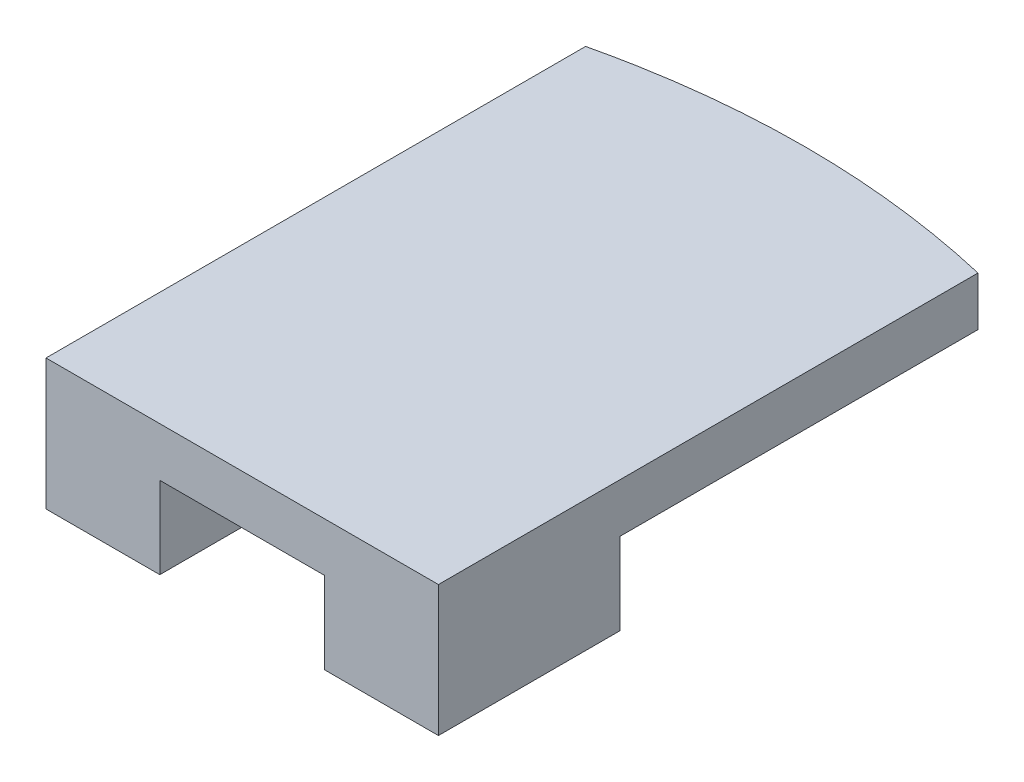
SolidWorks part; units mm, degrees
ref_plane "Front Plane" through (0, 0, 0) normal (0, 0, 1) x (1, 0, 0)
ref_plane "Top Plane" through (0, 0, 0) normal (0, 1, 0) x (1, 0, 0)
ref_plane "Right Plane" through (0, 0, 0) normal (1, 0, 0) x (0, 0, -1)
sketch "Sketch1" plane through (0, 0, 0) normal (0, 1, 0) x (1, 0, 0)
  line L0 (0, 0) -> (24, 0)
  line L1 (12, 0) -> (12, 35) construction
  line L2 (0, 0) -> (0, 33.6) construction
  line L3 (24, 0) -> (24, 33.6) construction
  line L4 (0, 0) -> (0, 33.6)
  line L5 (24, 0) -> (24, 33.6)
  spline S0 degree 2 poles (0, 33.6) (12, 36.4) (24, 33.6) knots 0 0 0 1 1 1
  dimension "D1" = 24
  dimension "D2" = 33.6
extrude "Boss-Extrude1" add sketch "Sketch1" along normal blind 3
sketch "Sketch4" plane through (0, 3, 0) normal (0, 1, 0) x (1, 0, 0)
  line L0 (24, 0) -> (24, 33.6) construction
  line L1 (0, 0) -> (24, 0)
  line L2 (0, 0) -> (0, 0.6)
  line L3 (0, 0.6) -> (24, 0.6)
  line L4 (24, 0) -> (24, 0.6)
  dimension "D1" = 0.6
extrude "Cut-Extrude3" cut sketch "Sketch4" against normal through all
sketch "Sketch5" plane through (0, 0, 0) normal (0, -1, 0) x (1, 0, 0)
  line L0 (12, -0.6) -> (12, -35) construction
  line L1 (0, -0.6) -> (6.96, -0.6)
  line L2 (0, -0.6) -> (0, -11.6948)
  line L3 (0, -11.6948) -> (6.96, -11.6948)
  line L4 (6.96, -0.6) -> (6.96, -11.6948)
  line L5 (24, -0.6) -> (0, -0.6) construction
  line L6 (24, -0.6) -> (17.04, -0.6)
  line L7 (24, -0.6) -> (24, -11.6948)
  line L8 (24, -11.6948) -> (17.04, -11.6948)
  line L9 (17.04, -0.6) -> (17.04, -11.6948)
  parabola Q0 (24, -33.6) -> (0, -33.6) focus (12, -9.2857) apex (12, -35) construction
extrude "Boss-Extrude2" add sketch "Sketch5" along normal blind 5
